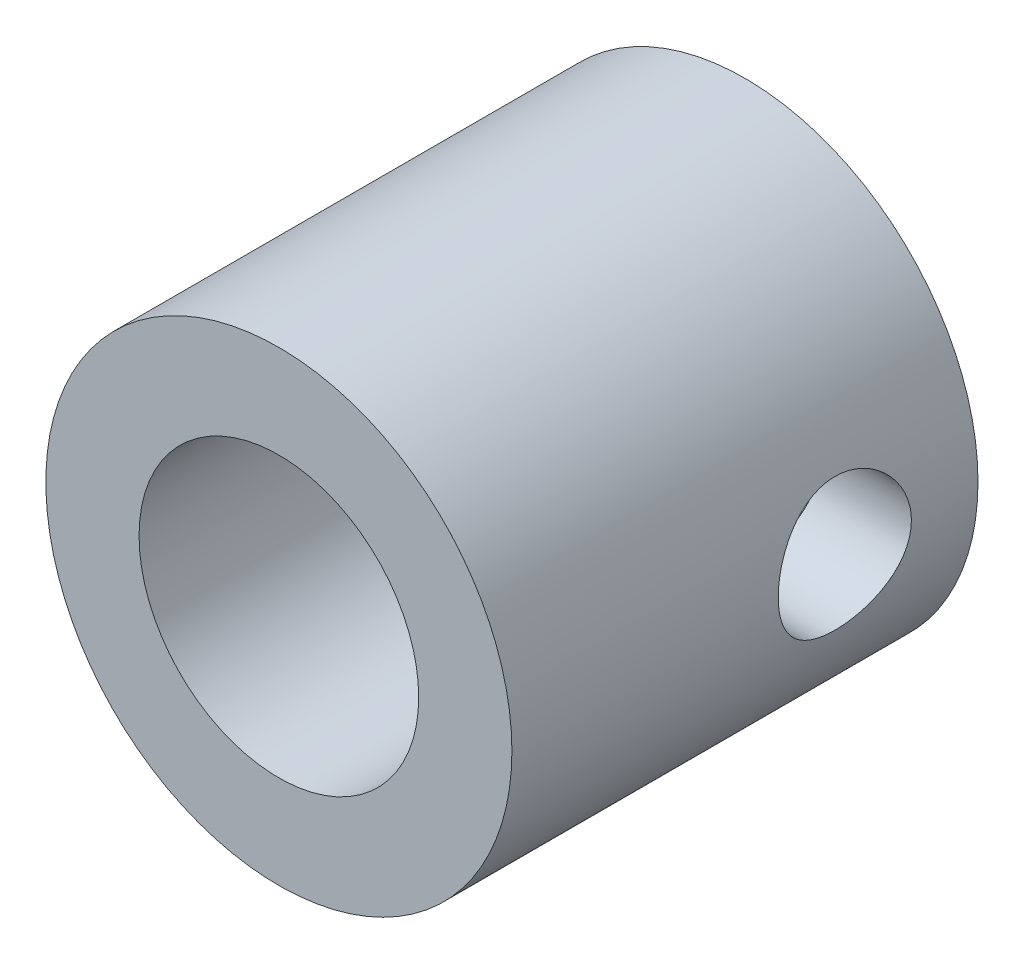
SolidWorks part; units mm, degrees
ref_plane "Front Plane" through (0, 0, 0) normal (0, 0, 1) x (1, 0, 0)
ref_plane "Top Plane" through (0, 0, 0) normal (0, 1, 0) x (1, 0, 0)
ref_plane "Right Plane" through (0, 0, 0) normal (1, 0, 0) x (0, 0, -1)
sketch "Sketch1" plane through (0, 0, 0) normal (0, 0, 1) x (1, 0, 0)
  circle A0 centre (0, 0) radius 2.1
  circle A1 centre (0, 0) radius 3.5
  dimension "D1" = 4.2
  dimension "D2" = 7
extrude "Boss-Extrude1" add sketch "Sketch1" along normal blind 7
ref_plane "Plane1" through (3.5, 0, 0) normal (1, 0, 0) x (0, 0, -1)
sketch "Sketch2" plane through (3.5, 0, 0) normal (1, 0, 0) x (0, 0, -1)
  line L0 (-7, 0) -> (0, 0) construction
  line L1 (-7, 3.5) -> (-7, -3.5) construction
  circle A0 centre (-2, 0) radius 1
  dimension "D1" = 2
  dimension "D2" = 5
extrude "Cut-Extrude1" cut sketch "Sketch2" against normal through all both and the other way through all
ref_plane "Plane2" through (-3.5, 0, 0) normal (-1, 0, 0) x (0, 0, 1)
sketch "Sketch3" plane through (-3.5, -1.6469, 0) normal (-1, 0, 0) x (0, 0.027, 0.9996)
  circle A0 centre (2.0437, 1.5924) radius 1
  circle A1 centre (2.0437, 1.5924) radius 1 construction
